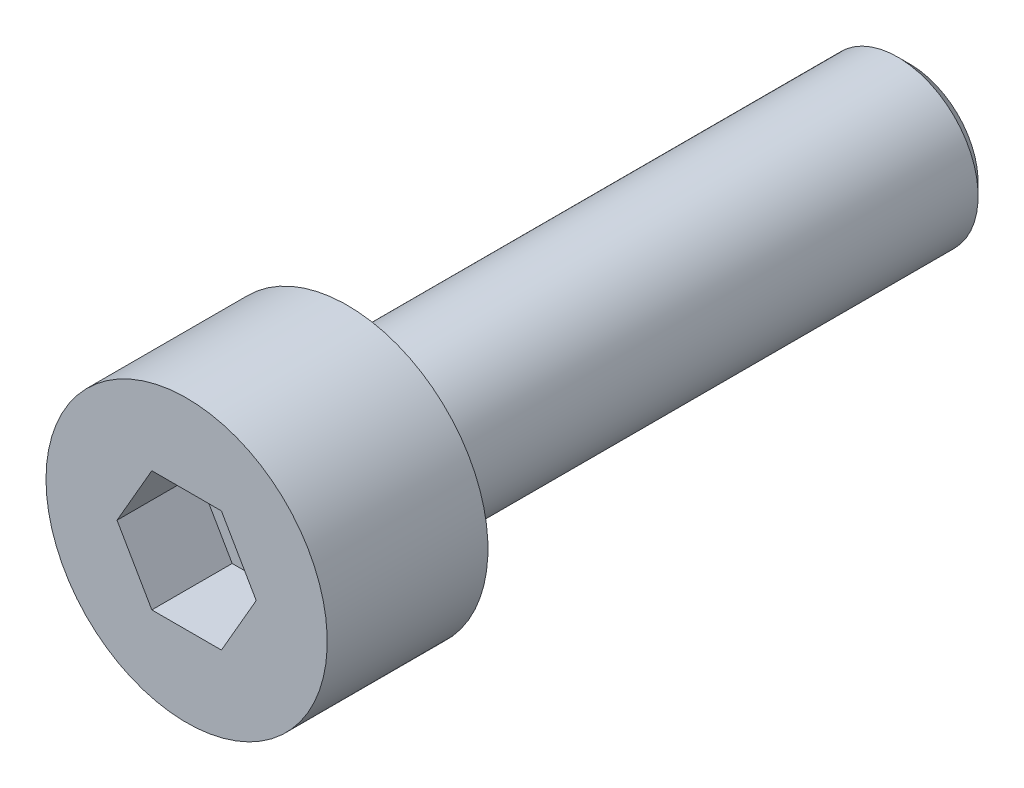
SolidWorks part; units mm, degrees
material "Простая углеродистая сталь"
ref_plane "Спереди" through (0, 0, 0) normal (0, 0, 1) x (1, 0, 0)
ref_plane "Сверху" through (0, 0, 0) normal (0, 1, 0) x (1, 0, 0)
ref_plane "Справа" through (0, 0, 0) normal (1, 0, 0) x (0, 0, -1)
sketch "Эскиз1" plane through (0, 0, 0) normal (1, 0, 0) x (0, 0, -1)
  line L0 (0, 0) -> (0, 3.5)
  line L1 (0, 3.5) -> (4, 3.5)
  line L2 (4, 3.5) -> (4, 2)
  line L3 (4, 2) -> (18, 2)
  line L4 (18, 2) -> (18, 0)
  line L5 (18, 0) -> (0, 0)
  line L6 (0, 0) -> (-1.7761, 0) construction
  dimension "D1" = 7
  dimension "D2" = 4
  dimension "D3" = 14
  dimension "D4" = 4
revolve "Повернуть1" add sketch "Эскиз1" angle 360 about L6
sketch "Эскиз2" plane through (0, 0, 0) normal (0, 0, 1) x (1, 0, 0)
  line L0 (0, 0) -> (0.8127, 0) construction
  line L1 (1.7321, 0) -> (0.866, 1.5)
  line L2 (0.866, 1.5) -> (-0.866, 1.5)
  line L3 (-0.866, 1.5) -> (-1.7321, 0)
  line L4 (-1.7321, 0) -> (-0.866, -1.5)
  line L5 (-0.866, -1.5) -> (0.866, -1.5)
  line L6 (0.866, -1.5) -> (1.7321, 0)
  circle A0 centre (0, 0) radius 1.5 construction
  dimension "D1" = 3
  dimension "D2" = 60
extrude "Вырез-Вытянуть1" cut sketch "Эскиз2" against normal blind 2
fillet "Скругление1" radius 0.3 1 edges at (-2, 0, -4)
chamfer "Фаска1" distance 0.3 angle 45 1 edges at (-2, 0, -18)
